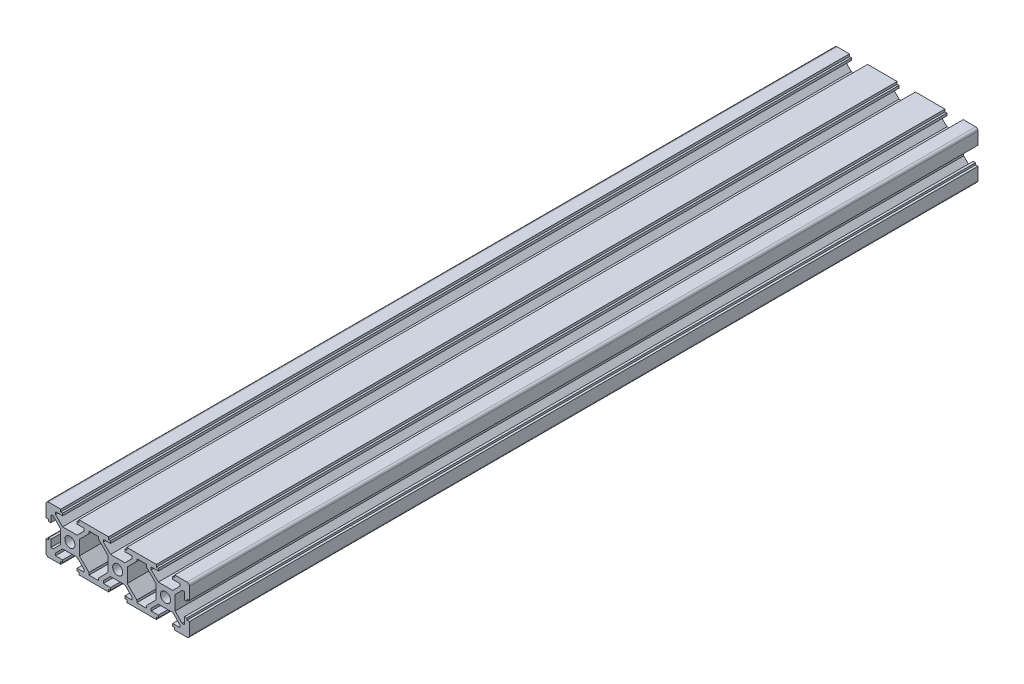
SolidWorks part; units mm, degrees
material "6061 合金"
ref_plane "前视基准面" through (0, 0, 0) normal (0, 0, 1) x (1, 0, 0)
ref_plane "上视基准面" through (0, 0, 0) normal (0, 1, 0) x (1, 0, 0)
ref_plane "右视基准面" through (0, 0, 0) normal (1, 0, 0) x (0, 0, -1)
sketch "草图1" plane through (0, 0, 0) normal (0, 0, 1) x (1, 0, 0)
  line L0 (-32.2486, -0.2298) -> (-32.2486, -1.031)
  line L1 (-32.2486, -1.031) -> (-33.25, -1.031)
  line L2 (-33.25, -1.031) -> (-33.25, -6.2384)
  line L3 (-32.2438, -7.2255) -> (-27.0786, -7.2255)
  line L4 (-27.0786, -7.2255) -> (-27.0786, -6.2241)
  line L5 (-27.0786, -6.2241) -> (-26.2774, -6.2241)
  line L6 (-26.2774, -6.2241) -> (-26.2774, -5.2127)
  line L7 (-26.2774, -5.2127) -> (-29.273, -5.2127)
  line L8 (-29.273, -5.2127) -> (-29.273, -4.2115)
  line L9 (-29.273, -4.2115) -> (-26.2796, -1.2254)
  line L10 (-26.2796, -1.2254) -> (-20.249, -1.2254)
  line L14 (-20.249, -1.2254) -> (-17.2556, -4.2115)
  line L15 (-17.2556, -4.2115) -> (-17.2556, -5.2127)
  line L16 (-17.2556, -5.2127) -> (-20.2513, -5.2127)
  line L17 (-20.2513, -5.2127) -> (-20.2513, -6.2241)
  line L18 (-20.2513, -6.2241) -> (-19.4501, -6.2241)
  line L19 (-19.4501, -6.2241) -> (-19.4501, -7.2255)
  line L20 (-19.4501, -7.2255) -> (-7.0642, -7.2255)
  line L21 (-7.0642, -7.2255) -> (-7.0642, -6.2241)
  line L22 (-7.0642, -6.2241) -> (-6.2631, -6.2241)
  line L23 (-6.2631, -6.2241) -> (-6.2631, -5.2127)
  line L24 (-6.2631, -5.2127) -> (-9.2587, -5.2127)
  line L25 (-9.2587, -5.2127) -> (-9.2587, -4.2115)
  line L26 (-9.2587, -4.2115) -> (-6.2653, -1.2254)
  line L27 (-6.2653, -1.2254) -> (-0.2347, -1.2254)
  line L31 (-0.2347, -1.2254) -> (2.7587, -4.2115)
  line L32 (2.7587, -4.2115) -> (2.7587, -5.2127)
  line L33 (2.7587, -5.2127) -> (-0.2369, -5.2127)
  line L34 (-0.2369, -5.2127) -> (-0.2369, -6.2241)
  line L35 (-0.2369, -6.2241) -> (0.5642, -6.2241)
  line L36 (0.5642, -6.2241) -> (0.5642, -7.2255)
  line L37 (0.5642, -7.2255) -> (12.9455, -7.2255)
  line L38 (12.9455, -7.2255) -> (12.9455, -6.2191)
  line L39 (12.9455, -6.2191) -> (13.7512, -6.2191)
  line L40 (13.7512, -6.2191) -> (13.7512, -5.2127)
  line L41 (13.7512, -5.2127) -> (10.7556, -5.2127)
  line L42 (10.7556, -5.2127) -> (10.7556, -4.2115)
  line L43 (10.7556, -4.2115) -> (13.749, -1.2254)
  line L44 (13.749, -1.2254) -> (19.7796, -1.2254)
  line L48 (19.7796, -1.2254) -> (22.773, -4.2115)
  line L49 (22.773, -4.2115) -> (22.773, -5.2127)
  line L50 (22.773, -5.2127) -> (19.7728, -5.2127)
  line L51 (19.7728, -5.2127) -> (19.7728, -6.2191)
  line L52 (19.7728, -6.2191) -> (20.5739, -6.2191)
  line L53 (20.5739, -6.2191) -> (20.5739, -7.2255)
  line L54 (20.5739, -7.2255) -> (25.7438, -7.2255)
  line L55 (26.75, -6.2384) -> (26.75, -1.031)
  line L56 (26.75, -1.031) -> (25.7485, -1.031)
  line L57 (25.7485, -1.031) -> (25.7485, -0.2298)
  line L58 (25.7485, -0.2298) -> (24.7613, -0.2298)
  line L59 (24.7613, -0.2298) -> (24.7613, -3.2342)
  line L60 (24.7613, -3.2342) -> (23.7599, -3.2342)
  line L61 (23.7599, -3.2342) -> (20.7701, -0.2372)
  line L65 (20.7701, -0.2372) -> (20.7701, 5.7861)
  line L66 (20.7701, 5.7861) -> (23.7599, 8.7832)
  line L67 (23.7599, 8.7832) -> (24.7613, 8.7832)
  line L68 (24.7613, 8.7832) -> (24.7613, 5.7788)
  line L69 (24.7613, 5.7788) -> (25.7485, 5.7788)
  line L70 (25.7485, 5.7788) -> (25.7485, 6.5799)
  line L71 (25.7485, 6.5799) -> (26.75, 6.5799)
  line L72 (26.75, 6.5799) -> (26.75, 11.7682)
  line L73 (25.7438, 12.7745) -> (20.5739, 12.7745)
  line L74 (20.5739, 12.7745) -> (20.5739, 11.7681)
  line L75 (20.5739, 11.7681) -> (19.7728, 11.7681)
  line L76 (19.7728, 11.7681) -> (19.7728, 10.7617)
  line L77 (19.7728, 10.7617) -> (22.773, 10.7617)
  line L78 (22.773, 10.7617) -> (22.773, 9.7604)
  line L79 (22.773, 9.7604) -> (19.7796, 6.7743)
  line L83 (19.7796, 6.7743) -> (13.749, 6.7743)
  line L84 (13.749, 6.7743) -> (10.7556, 9.7604)
  line L85 (10.7556, 9.7604) -> (10.7556, 10.7617)
  line L86 (10.7556, 10.7617) -> (13.7466, 10.7617)
  line L87 (13.7466, 10.7617) -> (13.7466, 11.7681)
  line L88 (13.7466, 11.7681) -> (12.9455, 11.7681)
  line L89 (12.9455, 11.7681) -> (12.9455, 12.7745)
  line L90 (12.9455, 12.7745) -> (0.5642, 12.7745)
  line L91 (0.5642, 12.7745) -> (0.5642, 11.773)
  line L92 (0.5642, 11.773) -> (-0.2369, 11.773)
  line L93 (-0.2369, 11.773) -> (-0.2369, 10.7617)
  line L94 (-0.2369, 10.7617) -> (2.7587, 10.7617)
  line L95 (2.7587, 10.7617) -> (2.7587, 9.7604)
  line L96 (2.7587, 9.7604) -> (-0.2347, 6.7743)
  line L100 (-0.2347, 6.7743) -> (-6.2653, 6.7743)
  line L101 (-6.2653, 6.7743) -> (-9.2587, 9.7604)
  line L102 (-9.2587, 9.7604) -> (-9.2587, 10.7617)
  line L103 (-9.2587, 10.7617) -> (-6.2631, 10.7617)
  line L104 (-6.2631, 10.7617) -> (-6.2631, 11.773)
  line L105 (-6.2631, 11.773) -> (-7.0642, 11.773)
  line L106 (-7.0642, 11.773) -> (-7.0642, 12.7745)
  line L107 (-7.0642, 12.7745) -> (-19.4501, 12.7745)
  line L108 (-19.4501, 12.7745) -> (-19.4501, 11.773)
  line L109 (-19.4501, 11.773) -> (-20.2513, 11.773)
  line L110 (-20.2513, 11.773) -> (-20.2513, 10.7617)
  line L111 (-20.2513, 10.7617) -> (-17.2556, 10.7617)
  line L112 (-17.2556, 10.7617) -> (-17.2556, 9.7604)
  line L113 (-17.2556, 9.7604) -> (-20.249, 6.7743)
  line L117 (-20.249, 6.7743) -> (-26.2796, 6.7743)
  line L118 (-26.2796, 6.7743) -> (-29.273, 9.7604)
  line L119 (-29.273, 9.7604) -> (-29.273, 10.7617)
  line L120 (-29.273, 10.7617) -> (-26.2774, 10.7617)
  line L121 (-26.2774, 10.7617) -> (-26.2774, 11.773)
  line L122 (-26.2774, 11.773) -> (-27.0786, 11.773)
  line L123 (-27.0786, 11.773) -> (-27.0786, 12.7745)
  line L124 (-27.0786, 12.7745) -> (-32.2438, 12.7745)
  line L125 (-33.25, 11.7682) -> (-33.25, 6.5608)
  line L126 (-33.25, 6.5608) -> (-32.2486, 6.5608)
  line L127 (-32.2486, 6.5608) -> (-32.2486, 5.7596)
  line L128 (-32.2486, 5.7596) -> (-31.2613, 5.7596)
  line L129 (-31.2613, 5.7596) -> (-31.2613, 8.764)
  line L130 (-31.2613, 8.764) -> (-30.2599, 8.764)
  line L131 (-30.2599, 8.764) -> (-27.2701, 5.767)
  line L135 (-27.2701, 5.767) -> (-27.2701, -0.2372)
  line L136 (-27.2701, -0.2372) -> (-30.2599, -3.2342)
  line L137 (-30.2599, -3.2342) -> (-31.2613, -3.2342)
  line L138 (-31.2613, -3.2342) -> (-31.2613, -0.2298)
  line L139 (-31.2613, -0.2298) -> (-32.2486, -0.2298)
  line L147 (-19.2585, 5.7861) -> (-19.2585, -0.2372)
  line L150 (-19.2585, -0.2372) -> (-15.2673, -4.2381)
  line L151 (-15.2673, -4.2381) -> (-15.2673, -5.2223)
  line L152 (-15.2673, -5.2223) -> (-11.247, -5.2223)
  line L153 (-11.247, -5.2223) -> (-11.247, -4.2381)
  line L154 (-11.247, -4.2381) -> (-7.2558, -0.2372)
  line L155 (-7.2558, -0.2372) -> (-7.2558, 2.7745)
  line L156 (-7.2558, 2.7745) -> (-7.2558, 5.7861)
  line L157 (-7.2558, 5.7861) -> (-11.247, 9.787)
  line L158 (-11.247, 9.787) -> (-11.247, 10.7712)
  line L159 (-11.247, 10.7712) -> (-15.2673, 10.7712)
  line L160 (-15.2673, 10.7712) -> (-15.2673, 9.787)
  line L161 (-15.2673, 9.787) -> (-19.2585, 5.7861)
  line L162 (4.747, -5.2223) -> (8.7673, -5.2223)
  line L163 (8.7673, -5.2223) -> (8.7673, -4.2381)
  line L164 (8.7673, -4.2381) -> (12.7585, -0.2372)
  line L165 (12.7585, -0.2372) -> (12.7585, 2.7745)
  line L166 (12.7585, 2.7745) -> (12.7585, 5.7861)
  line L167 (12.7585, 5.7861) -> (8.7673, 9.787)
  line L168 (8.7673, 9.787) -> (8.7673, 10.7712)
  line L169 (8.7673, 10.7712) -> (4.747, 10.7712)
  line L170 (4.747, 10.7712) -> (4.747, 9.787)
  line L171 (4.747, 9.787) -> (0.7558, 5.7861)
  line L172 (0.7558, 5.7861) -> (0.7558, 2.7745)
  line L173 (0.7558, 2.7745) -> (0.7558, -0.2372)
  line L174 (0.7558, -0.2372) -> (4.747, -4.2381)
  line L175 (4.747, -4.2381) -> (4.747, -5.2223)
  line L176 (-23.25, 2.7745) -> (-23.25, 12.5158) construction
  line L177 (-23.25, 2.7745) -> (-33.2945, 2.7745) construction
  line L178 (-23.25, 2.7745) -> (-23.25, -7.2784) construction
  line L179 (-23.25, 2.7745) -> (-17.6462, 2.7745) construction
  line L180 (-3.25, 2.7745) -> (-3.25, 12.9074) construction
  line L181 (-3.25, 2.7745) -> (-3.25, -7.2598) construction
  line L182 (-3.25, 2.7745) -> (-8.8035, 2.7745) construction
  line L183 (-3.25, 2.7745) -> (2.4087, 2.7745) construction
  line L184 (16.75, 2.7745) -> (16.75, 12.9038) construction
  line L185 (16.75, 2.7745) -> (26.8187, 2.7745) construction
  line L186 (16.75, 2.7745) -> (16.75, -7.3953) construction
  line L187 (16.75, 2.7745) -> (10.7407, 2.7745) construction
  circle A0 centre (-3.25, 2.7745) radius 2.103
  circle A1 centre (-23.25, 2.7745) radius 2.103
  circle A2 centre (16.75, 2.7745) radius 2.103
  arc A3 (-33.25, -6.2384) -> (-32.2438, -7.2255) centre (-32.2487, -6.2241) ccw
  arc A4 (25.7438, -7.2255) -> (26.75, -6.2384) centre (25.7487, -6.2241) ccw
  arc A5 (26.75, 11.7682) -> (25.7438, 12.7745) centre (25.7486, 11.773) ccw
  arc A6 (-32.2438, 12.7745) -> (-33.25, 11.7682) centre (-32.2486, 11.773) ccw
  point P197 (-29.6612, 12.7745)
  dimension "D1" = 60
  dimension "D2" = 20
  dimension "D3" = 20
  dimension "D4" = 20
  dimension "D5" = 10
  dimension "D6" = 10
  dimension "D7" = 10
  dimension "D8" = 10
extrude "凸台-拉伸1" add sketch "草图1" along normal blind 330
